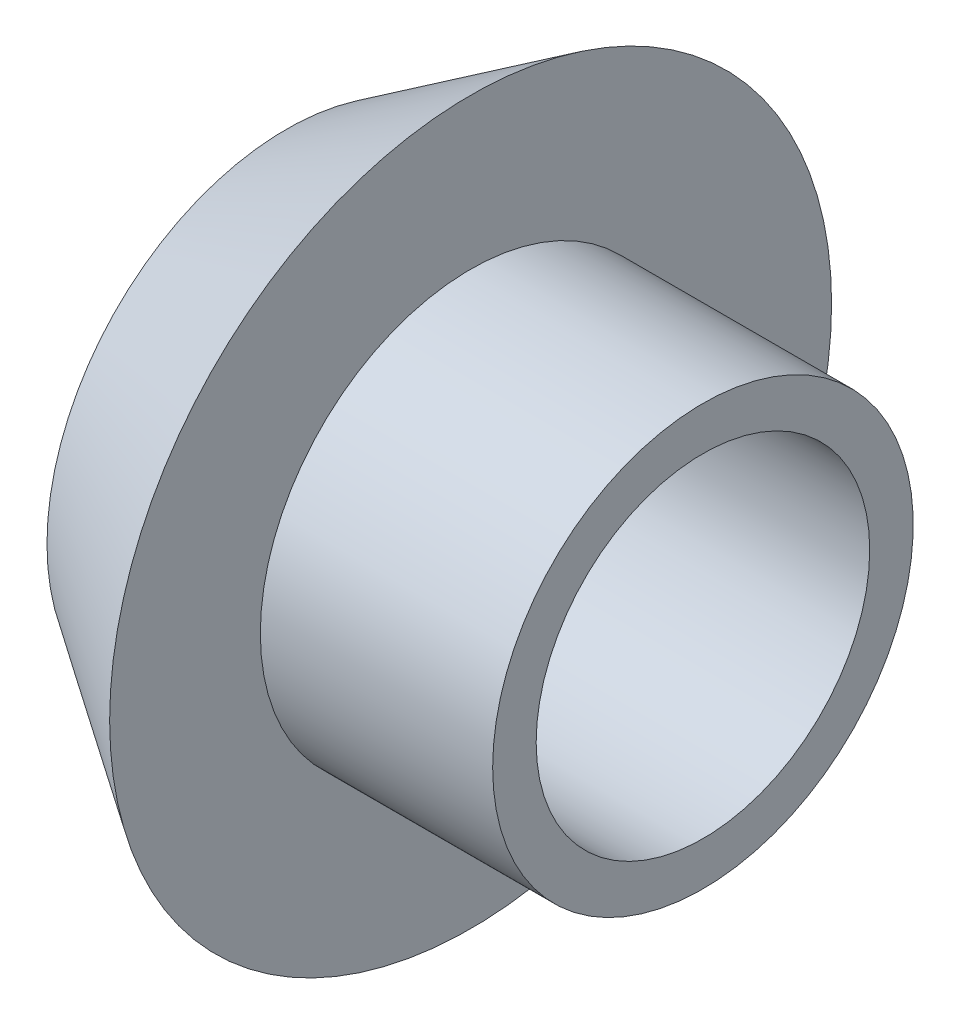
SolidWorks part; units mm, degrees
material "AISI 1045 Steel, cold drawn"
ref_plane "Front Plane" through (0, 0, 0) normal (0, 0, 1) x (1, 0, 0)
ref_plane "Top Plane" through (0, 0, 0) normal (0, 1, 0) x (1, 0, 0)
ref_plane "Right Plane" through (0, 0, 0) normal (1, 0, 0) x (0, 0, -1)
sketch "Sketch3" plane through (0, 0, 0) normal (0, 0, 1) x (1, 0, 0)
  line L0 (-14.36, 0) -> (14.36, 0) construction
  line L1 (-14.36, 0) -> (-14.36, 16.51) construction
  line L2 (-14.36, 0) -> (-1.66, 0) construction
  line L3 (-1.66, 0) -> (-1.66, 24.89) construction
  line L4 (-14.36, 16.51) -> (-1.66, 24.89)
  line L5 (-1.66, 24.89) -> (-1.66, 14.5)
  line L6 (-1.66, 14.5) -> (14.36, 14.5)
  line L7 (14.36, 14.5) -> (14.36, 11.5)
  line L8 (14.36, 11.5) -> (-14.36, 11.5)
  line L9 (-14.36, 11.5) -> (-14.36, 16.51)
  dimension "D1" = 28.72
  dimension "D2" = 16.51
  dimension "D3" = 12.7
  dimension "D4" = 24.89
  dimension "D5" = 14.5
  dimension "D6" = 11.5
revolve "Revolve1" add sketch "Sketch3" angle 360 about L0
